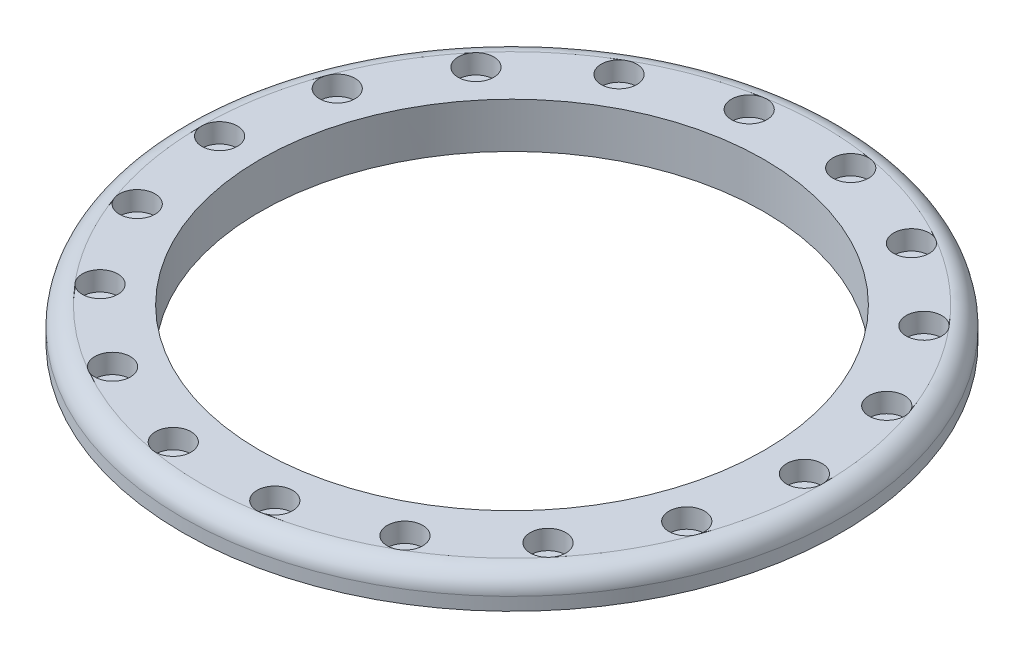
SolidWorks part; units mm, degrees
material "ABS"
ref_plane "Front Plane" through (0, 0, 0) normal (0, 0, 1) x (1, 0, 0)
ref_plane "Top Plane" through (0, 0, 0) normal (0, 1, 0) x (1, 0, 0)
ref_plane "Right Plane" through (0, 0, 0) normal (1, 0, 0) x (0, 0, -1)
sketch "Sketch1" plane through (0, 0, 0) normal (0, 1, 0) x (1, 0, 0)
  line L0 (0, 0) -> (51, 0) construction
  circle A0 centre (0, 0) radius 51
  circle A1 centre (0, 0) radius 39
  circle A2 centre (45.25, 0) radius 1.5
  circle A3 centre (42.5211, -15.4764) radius 1.5
  circle A4 centre (34.6635, -29.0861) radius 1.5
  circle A5 centre (22.625, -39.1876) radius 1.5
  circle A6 centre (7.8576, -44.5626) radius 1.5
  circle A7 centre (-7.8576, -44.5626) radius 1.5
  circle A8 centre (-22.625, -39.1876) radius 1.5
  circle A9 centre (-34.6635, -29.0861) radius 1.5
  circle A10 centre (-42.5211, -15.4764) radius 1.5
  circle A11 centre (-45.25, 0) radius 1.5
  circle A12 centre (-42.5211, 15.4764) radius 1.5
  circle A13 centre (-34.6635, 29.0861) radius 1.5
  circle A14 centre (-22.625, 39.1876) radius 1.5
  circle A15 centre (-7.8576, 44.5626) radius 1.5
  circle A16 centre (7.8576, 44.5626) radius 1.5
  circle A17 centre (22.625, 39.1876) radius 1.5
  circle A18 centre (34.6635, 29.0861) radius 1.5
  circle A19 centre (42.5211, 15.4764) radius 1.5
  point P43 (0, 0)
  dimension "D1" = 102
  dimension "D2" = 12
  dimension "D4" = 3
  dimension "D3" = 45.25
  dimension "D5" = 18
extrude "Boss-Extrude1" add sketch "Sketch1" along normal blind 5
fillet "Fillet1" radius 3 1 edges at (0, 5, 51)
sketch "Sketch2" plane through (0, 5, 0) normal (0, 1, 0) x (1, 0, 0)
  circle A0 centre (45.25, 0) radius 2.75
  circle A1 centre (42.5211, -15.4764) radius 2.75
  circle A2 centre (34.6635, -29.0861) radius 2.75
  circle A3 centre (22.625, -39.1876) radius 2.75
  circle A4 centre (7.8576, -44.5626) radius 2.75
  circle A5 centre (-7.8576, -44.5626) radius 2.75
  circle A6 centre (-22.625, -39.1876) radius 2.75
  circle A7 centre (-34.6635, -29.0861) radius 2.75
  circle A8 centre (-42.5211, -15.4764) radius 2.75
  circle A9 centre (-45.25, 0) radius 2.75
  circle A10 centre (-42.5211, 15.4764) radius 2.75
  circle A11 centre (-34.6635, 29.0861) radius 2.75
  circle A12 centre (-22.625, 39.1876) radius 2.75
  circle A13 centre (-7.8576, 44.5626) radius 2.75
  circle A14 centre (7.8576, 44.5626) radius 2.75
  circle A15 centre (22.625, 39.1876) radius 2.75
  circle A16 centre (34.6635, 29.0861) radius 2.75
  circle A17 centre (42.5211, 15.4764) radius 2.75
  point P4 (42.9362, 15.7846)
  point P5 (42.5211, 15.4764)
  point P39 (0, 0)
  point P41 (42.9362, 15.7846)
  dimension "D1" = 5.5
  dimension "D2" = 18
extrude "Cut-Extrude1" cut sketch "Sketch2" against normal blind 3
sketch "Sketch3" plane through (0, 0, 0) normal (0, -1, 0) x (1, 0, 0)
  circle A0 centre (0, 0) radius 39
  circle A1 centre (0, 0) radius 41.5
  dimension "D1" = 2.5
extrude "Boss-Extrude2" add sketch "Sketch3" along normal blind 2
